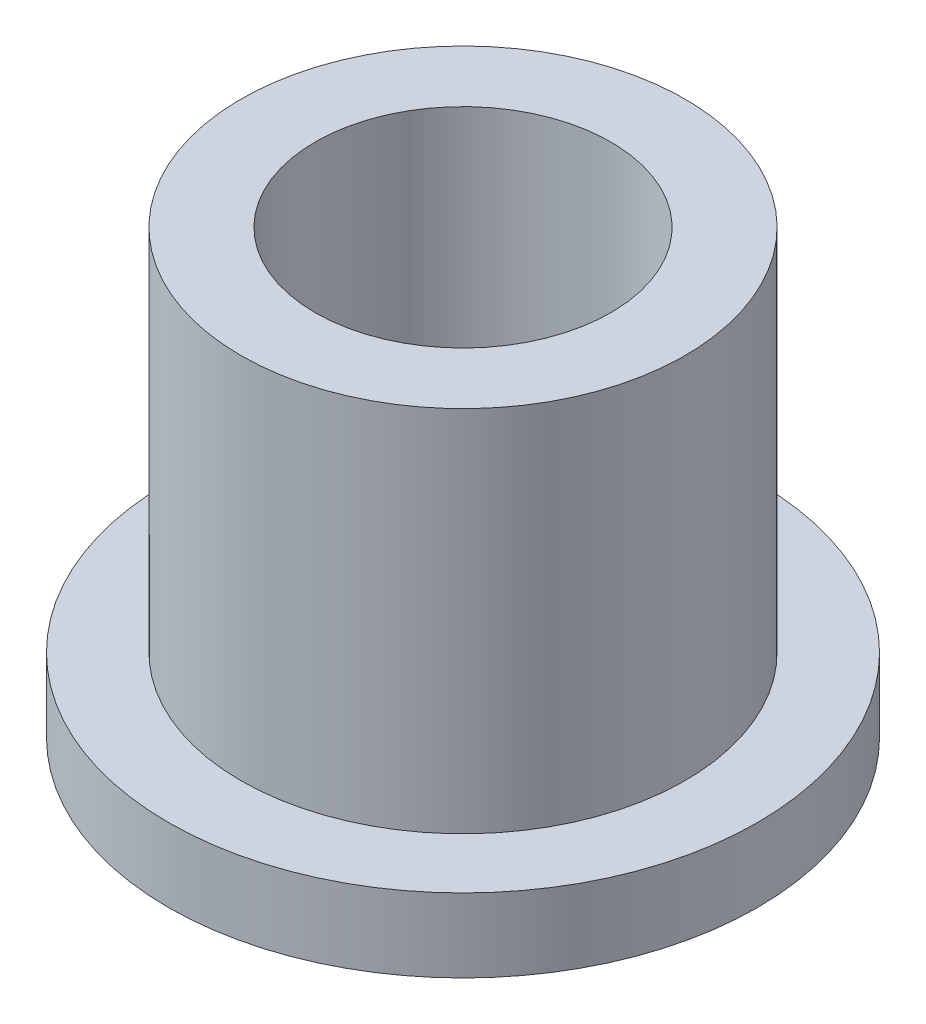
SolidWorks part; units mm, degrees
material "Tin Bearing Bronze"
ref_plane "Front" through (0, 0, 0) normal (0, 0, 1) x (1, 0, 0)
ref_plane "Top" through (0, 0, 0) normal (0, 1, 0) x (1, 0, 0)
ref_plane "Right" through (0, 0, 0) normal (1, 0, 0) x (0, 0, -1)
sketch "Sketch1" plane through (0, 0, 0) normal (0, 1, 0) x (1, 0, 0)
  circle A0 centre (0, 0) radius 3.1877
  circle A1 centre (0, 0) radius 4.7879
  circle A2 centre (0, 0) radius 6.35
  dimension "ID" = 6.3754
  dimension "OD" = 9.5758
  dimension "FlangeOD" = 12.7
sketch "Sketch2" plane through (0, 0, 0) normal (0, 1, 0) x (1, 0, 0)
  circle A0 centre (0, 0) radius 3.1877 construction
  circle A1 centre (0, 0) radius 4.7879 construction
  circle A2 centre (0, 0) radius 3.1877
  circle A3 centre (0, 0) radius 4.7879
extrude "Boss-Extrude1" add sketch "Sketch2" along normal blind 9.525
sketch "Sketch3" plane through (0, 0, 0) normal (0, 1, 0) x (1, 0, 0)
  circle A0 centre (0, 0) radius 6.35 construction
  circle A1 centre (0, 0) radius 4.7879 construction
  circle A2 centre (0, 0) radius 6.35
  circle A3 centre (0, 0) radius 4.7879
extrude "Boss-Extrude2" add sketch "Sketch3" along normal blind 1.5875
